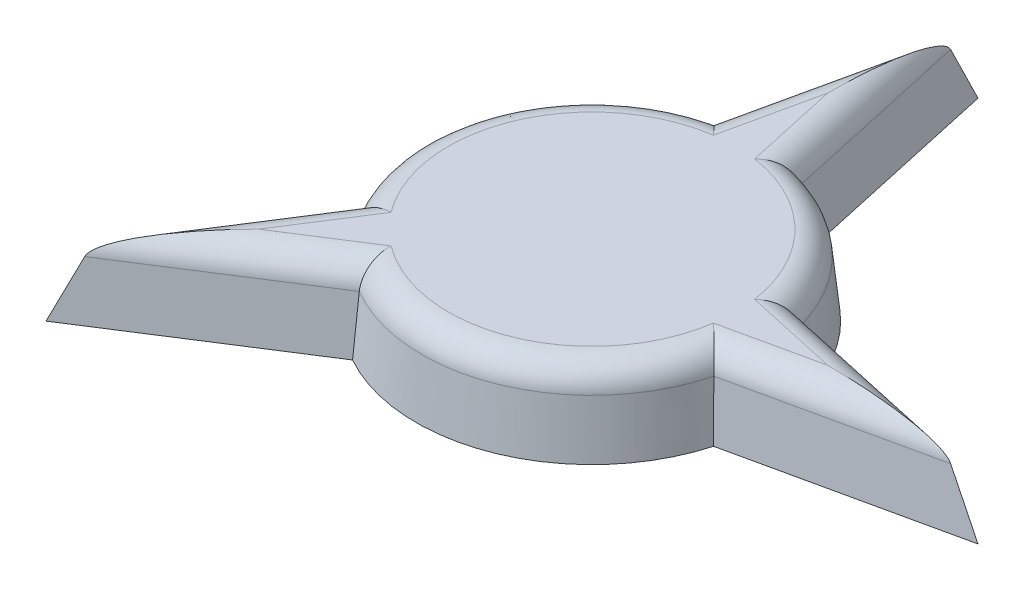
SolidWorks part; units mm, degrees
material "ABS"
ref_plane "Front Plane" through (0, 0, 0) normal (0, 0, 1) x (1, 0, 0)
ref_plane "Top Plane" through (0, 0, 0) normal (0, 1, 0) x (1, 0, 0)
ref_plane "Right Plane" through (0, 0, 0) normal (1, 0, 0) x (0, 0, -1)
sketch "Sketch1" plane through (0, 0, 0) normal (0, 1, 0) x (1, 0, 0)
  line L1 (-17.5, 17.5) -> (17.5, 17.5)
  line L2 (-17.5, 17.5) -> (-17.5, -17.5)
  line L3 (-17.5, -17.5) -> (17.5, -17.5)
  line L4 (17.5, 17.5) -> (17.5, -17.5)
  line L5 (-17.5, 17.5) -> (17.5, -17.5) construction
  line L6 (-17.5, -17.5) -> (17.5, 17.5) construction
  point P0 (0, 0)
  dimension "D1" = 35
sketch "Sketch2" plane through (0, 0, 0) normal (0, 1, 0) x (1, 0, 0)
  line L0 (0, 14.5436) -> (-1.795, 6.3768)
  line L1 (0, 14.5436) -> (0, 6.6246) construction
  line L2 (0, 14.5436) -> (1.795, 6.3768)
  line L5 (14.5436, 0) -> (6.3768, 1.795)
  line L6 (14.5436, 0) -> (6.3768, -1.795)
  line L11 (-10.2839, -10.2839) -> (-3.2399, -5.7783)
  line L12 (-10.2839, -10.2839) -> (-5.7783, -3.2399)
  line L17 (0, -14.5436) -> (1.795, -6.3768) [skipped]
  line L18 (0, -14.5436) -> (-1.795, -6.3768) [skipped]
  line L19 (-14.5436, 0) -> (-6.3768, -1.795) [skipped]
  line L20 (-14.5436, 0) -> (-6.3768, 1.795) [skipped]
  line L21 (10.2839, -10.2839) -> (5.7783, -3.2399) [skipped]
  line L22 (10.2839, -10.2839) -> (3.2399, -5.7783) [skipped]
  line L23 (-10.2839, 10.2839) -> (-3.2399, 5.7783) [skipped]
  line L24 (-10.2839, 10.2839) -> (-5.7783, 3.2399) [skipped]
  line L25 (10.2839, 10.2839) -> (3.2399, 5.7783) [skipped]
  line L26 (10.2839, 10.2839) -> (5.7783, 3.2399) [skipped]
  circle A0 centre (0, 0) radius 6.6246
  point P31 (0, 0)
  dimension "D1" = 8
extrude "Boss-Extrude1" add sketch "Sketch2" along normal blind 3 draft 6
fillet "Fillet1" radius 1 9 edges at (-5.8291, 3, -2.4145) (-0.7641, 3, -9.5981) (0.7641, 3, -9.5981) (4.4614, 3, -4.4614) (9.5981, 3, -0.7641) (9.5981, 3, 0.7641) (2.4145, 3, 5.8291) (-6.2466, 3, 7.3272) (-7.3272, 3, 6.2466)
